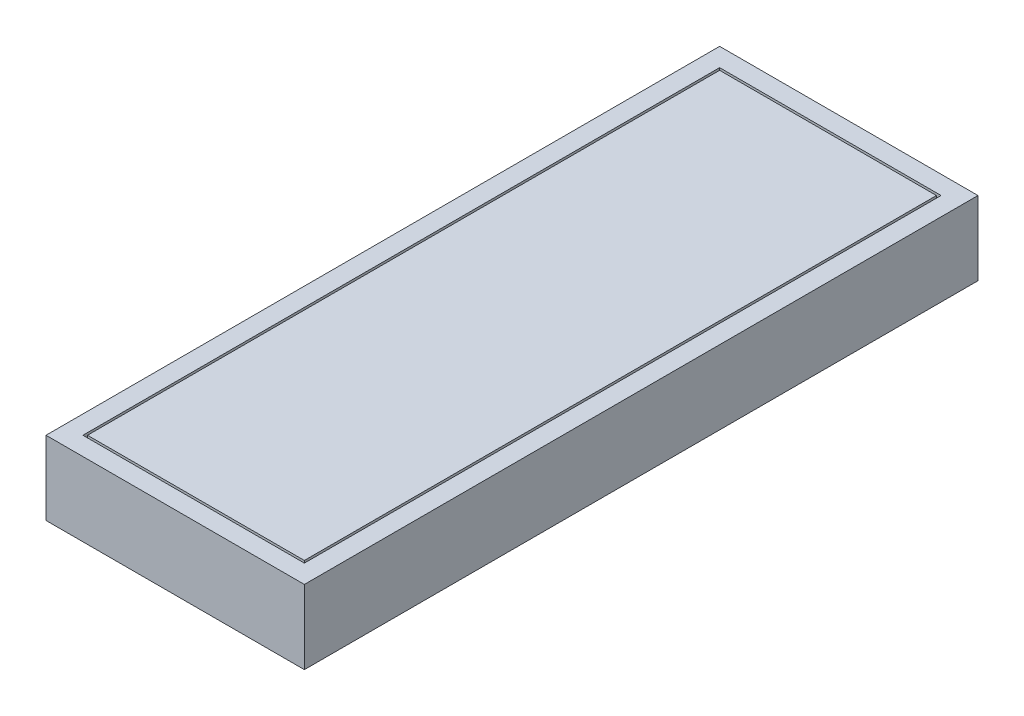
SolidWorks part; units mm, degrees
ref_plane "Front Plane" through (0, 0, 0) normal (0, 0, 1) x (1, 0, 0)
ref_plane "Top Plane" through (0, 0, 0) normal (0, 1, 0) x (1, 0, 0)
ref_plane "Right Plane" through (0, 0, 0) normal (1, 0, 0) x (0, 0, -1)
ref_plane "Plane1" through (0, -60, 0) normal (0, -1, 0) x (1, 0, 0)
sketch "Sketch1" plane through (0, -60, 0) normal (0, -1, 0) x (1, 0, 0)
  line L0 (-140, 0) -> (140, 0)
  line L1 (140, 0) -> (140, 730)
  line L2 (140, 730) -> (-140, 730)
  line L3 (-140, 730) -> (-140, 0)
  dimension "D1" = 730
  dimension "D2" = 140
  dimension "D3" = 280
extrude "Boss-Extrude1" add sketch "Sketch1" against normal blind 80
sketch "Sketch2" plane through (0, 20, 0) normal (0, 1, 0) x (-1, 0, 0)
  line L0 (120, 710) -> (-120, 710)
  line L1 (-120, 710) -> (-120, 20)
  line L2 (-120, 20) -> (120, 20)
  line L3 (120, 20) -> (120, 710)
  dimension "D1" = 20
  dimension "D2" = 690
  dimension "D3" = 120
  dimension "D4" = 240
extrude "Cut-Extrude1" cut sketch "Sketch2" against normal blind 11
sketch "Sketch3" plane through (0, 9, 0) normal (0, 1, 0) x (-1, 0, 0)
  line L0 (117.5, 707.5) -> (117.5, 22.5)
  line L1 (117.5, 22.5) -> (-117.5, 22.5)
  line L2 (-117.5, 22.5) -> (-117.5, 707.5)
  line L3 (-117.5, 707.5) -> (117.5, 707.5)
  line L4 (-120, 20) -> (120, 20) construction
  line L5 (120, 20) -> (120, 710) construction
  dimension "D1" = 2.5
  dimension "D2" = 685
  dimension "D3" = 2.5
  dimension "D4" = 235
extrude "Boss-Extrude2" add sketch "Sketch3" along normal blind 11
